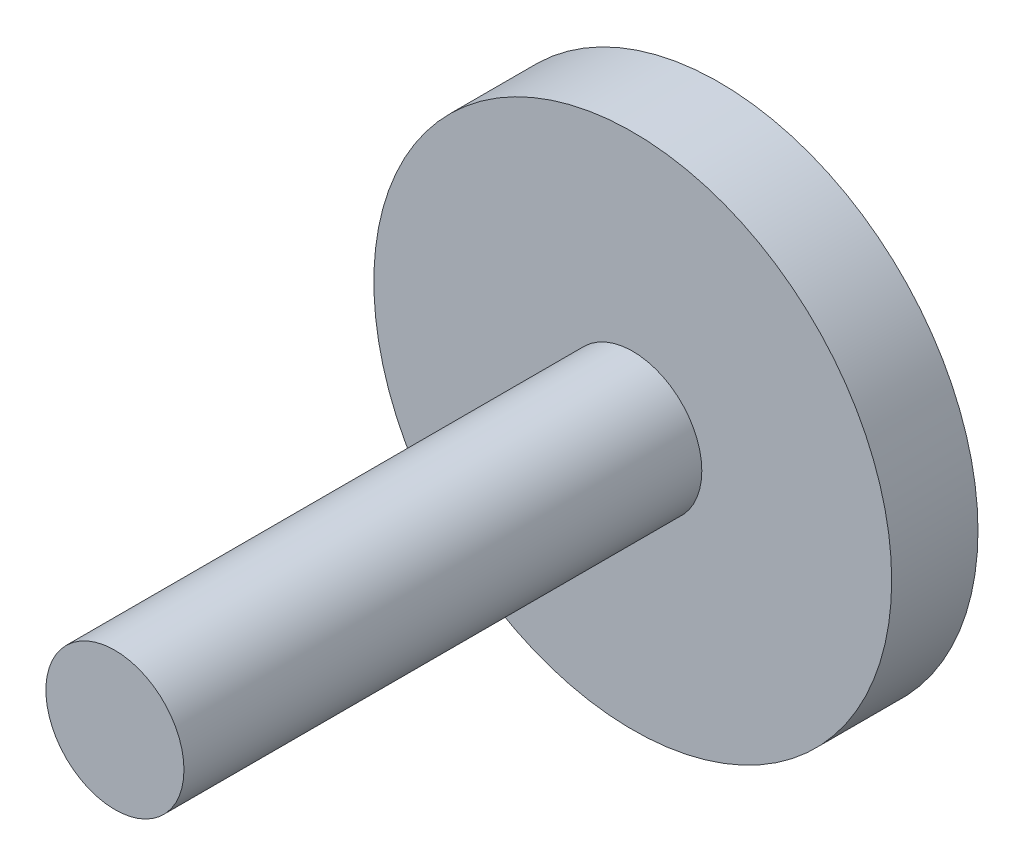
SolidWorks part; units mm, degrees
ref_plane "Спереди" through (0, 0, 0) normal (0, 0, 1) x (1, 0, 0)
ref_plane "Сверху" through (0, 0, 0) normal (0, 1, 0) x (1, 0, 0)
ref_plane "Справа" through (0, 0, 0) normal (1, 0, 0) x (0, 0, -1)
sketch "Эскиз1" plane through (0, 0, 0) normal (0, 0, 1) x (1, 0, 0)
  circle A0 centre (0, 0) radius 15
extrude "Бобышка-Вытянуть1" add sketch "Эскиз1" along normal blind 5
sketch "Эскиз2" plane through (0, 0, 5) normal (0, 0, 1) x (1, 0, 0)
  circle A0 centre (0, 0) radius 4
extrude "Бобышка-Вытянуть2" add sketch "Эскиз2" along normal blind 30
